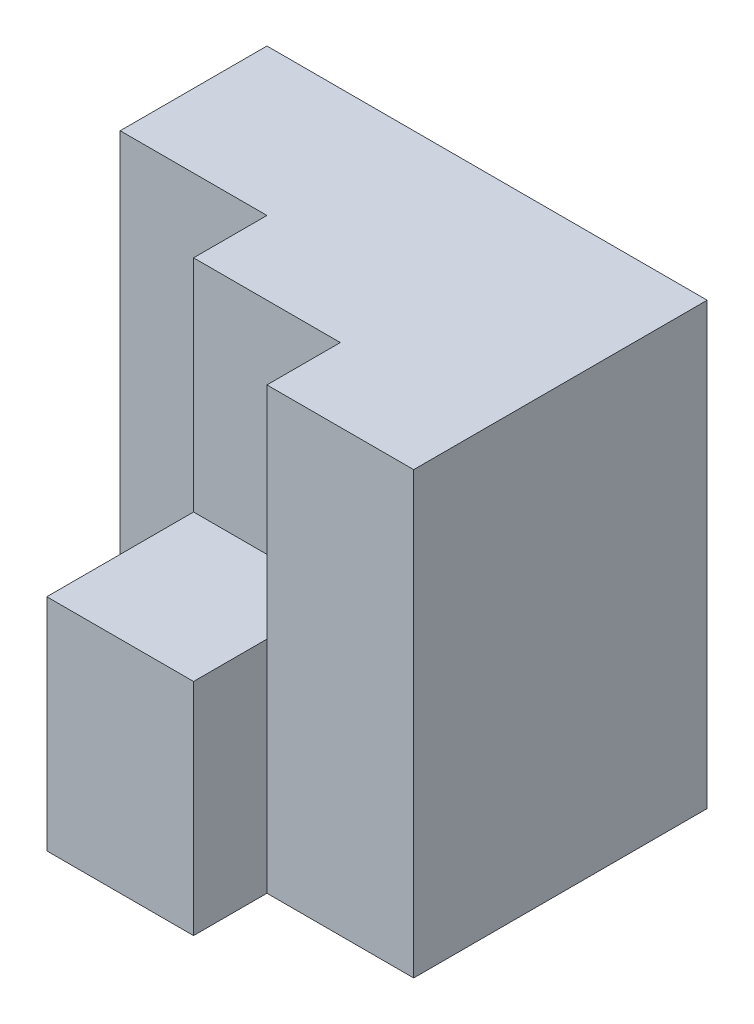
SolidWorks part; units mm, degrees
ref_plane "Front Plane" through (0, 0, 0) normal (0, 0, 1) x (1, 0, 0)
ref_plane "Top Plane" through (0, 0, 0) normal (0, 1, 0) x (1, 0, 0)
ref_plane "Right Plane" through (0, 0, 0) normal (1, 0, 0) x (0, 0, -1)
sketch "Sketch1" plane through (0, 0, 0) normal (0, 0, 1) x (1, 0, 0)
  line L1 (0, 0) -> (30, 0)
  line L2 (0, 0) -> (0, 30)
  line L3 (0, 30) -> (30, 30)
  line L4 (30, 0) -> (30, 30)
  dimension "D1" = 30
  dimension "D2" = 30
extrude "Boss-Extrude1" add sketch "Sketch1" along normal blind 25
sketch "Sketch2" plane through (0, 0, 25) normal (0, 0, 1) x (1, 0, 0)
  line L0 (30, 30) -> (0, 30) construction
  line L1 (30, 0) -> (20, 0)
  line L2 (30, 0) -> (30, 30)
  line L3 (30, 30) -> (20, 30)
  line L4 (20, 0) -> (20, 30)
  dimension "D1" = 10
extrude "Cut-Extrude1" cut sketch "Sketch2" against normal blind 5
sketch "Sketch3" plane through (0, 0, 25) normal (0, 0, 1) x (1, 0, 0)
  line L0 (20, 30) -> (0, 30) construction
  line L1 (0, 0) -> (10, 0)
  line L2 (0, 0) -> (0, 30)
  line L3 (0, 30) -> (10, 30)
  line L4 (10, 0) -> (10, 30)
  dimension "D1" = 10
extrude "Cut-Extrude2" cut sketch "Sketch3" against normal blind 15
sketch "Sketch4" plane through (0, 30, 0) normal (0, 1, 0) x (1, 0, 0)
  line L0 (10, -10) -> (10, -25) construction
  line L1 (20, -25) -> (10, -25)
  line L2 (20, -25) -> (20, -15)
  line L3 (20, -15) -> (10, -15)
  line L4 (10, -25) -> (10, -15)
  dimension "D1" = 10
extrude "Cut-Extrude3" cut sketch "Sketch4" against normal blind 15
